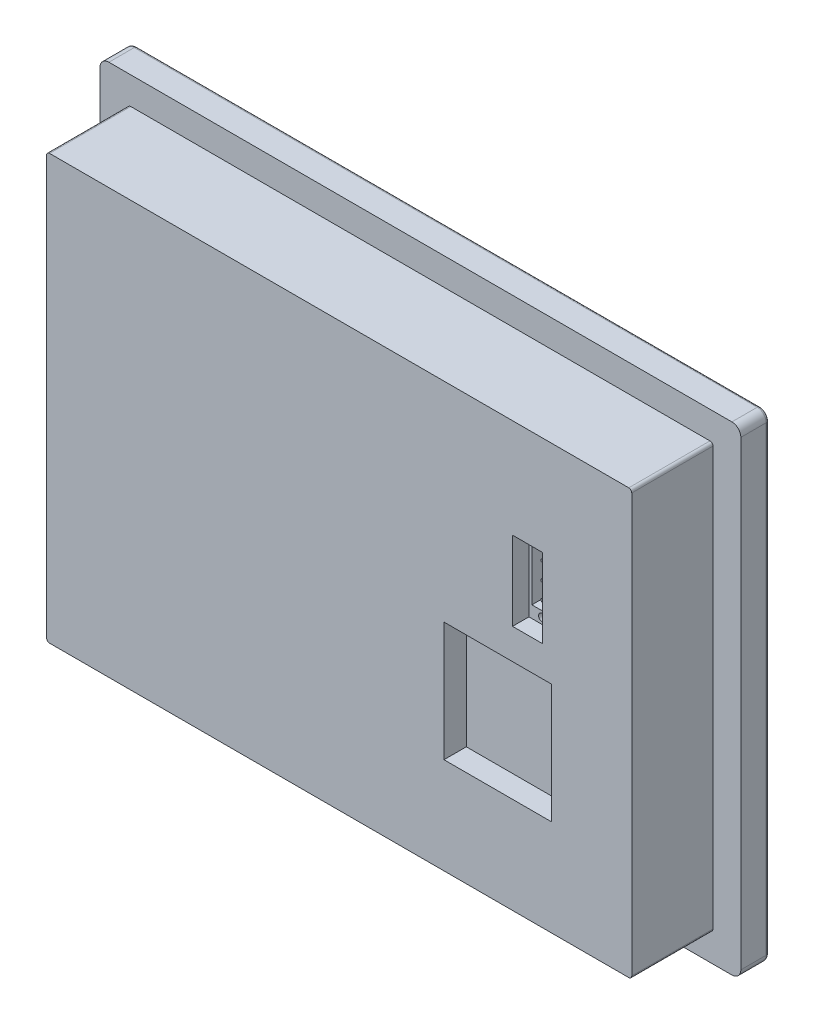
SolidWorks part; units mm, degrees
ref_plane "Ön Düzlem" through (0, 0, 0) normal (0, 0, 1) x (1, 0, 0)
ref_plane "Üst Düzlem" through (0, 0, 0) normal (0, 1, 0) x (1, 0, 0)
ref_plane "Sağ Düzlem" through (0, 0, 0) normal (1, 0, 0) x (0, 0, -1)
sketch "Çizim1" plane through (0, 0, 0) normal (0, 0, 1) x (1, 0, 0)
  line L1 (-107.5, 80.35) -> (107.5, 80.35)
  line L2 (-107.5, 80.35) -> (-107.5, -80.35)
  line L3 (-107.5, -80.35) -> (107.5, -80.35)
  line L4 (107.5, 80.35) -> (107.5, -80.35)
  line L5 (-107.5, 80.35) -> (107.5, -80.35) construction
  line L6 (-107.5, -80.35) -> (107.5, 80.35) construction
  point P0 (0, 0)
  dimension "D1" = 215
  dimension "D2" = 160.7
extrude "Yükseklik-Ekstrüzyon1" add sketch "Çizim1" along normal blind 9.5
sketch "Çizim2" plane through (0, 0, 9.5) normal (0, 0, 1) x (1, 0, 0)
  line L1 (-98.15, 71.15) -> (98.15, 71.15)
  line L2 (-98.15, 71.15) -> (-98.15, -71.15)
  line L3 (-98.15, -71.15) -> (98.15, -71.15)
  line L4 (98.15, 71.15) -> (98.15, -71.15)
  line L5 (-98.15, 71.15) -> (98.15, -71.15) construction
  line L6 (-98.15, -71.15) -> (98.15, 71.15) construction
  point P0 (0, 0)
  dimension "D1" = 196.3
  dimension "D2" = 142.3
extrude "Yükseklik-Ekstrüzyon2" add sketch "Çizim2" along normal blind 27.24
sketch "Çizim3" plane through (0, 0, 36.74) normal (0, 0, 1) x (1, 0, 0)
  line L1 (58.15, 37.9) -> (68.15, 37.9)
  line L2 (58.15, 37.9) -> (58.15, 11.4)
  line L3 (58.15, 11.4) -> (68.15, 11.4)
  line L4 (68.15, 37.9) -> (68.15, 11.4)
  line L5 (58.15, 37.9) -> (68.15, 11.4) construction
  line L6 (58.15, 11.4) -> (68.15, 37.9) construction
  line L7 (98.15, 71.15) -> (-98.15, 71.15) construction
  line L8 (98.15, -71.15) -> (98.15, 71.15) construction
  line L9 (58.65, 37.4) -> (67.65, 37.4)
  line L10 (67.65, 37.4) -> (67.65, 11.9)
  line L11 (58.65, 11.9) -> (67.65, 11.9)
  line L12 (58.65, 37.4) -> (58.65, 11.9)
  point P0 (63.15, 24.65)
  dimension "D1" = 46.5
  dimension "D2" = 35
  dimension "D3" = 10
  dimension "D4" = 26.5
  dimension "D5" = 0.5
extrude "Kes-Ekstrüzyon1" cut sketch "Çizim3" against normal blind 15
sketch "Çizim4" plane through (0, 0, 36.74) normal (0, 0, 1) x (1, 0, 0)
  line L4 (67.65, 37.4) -> (58.65, 37.4)
  line L5 (58.65, 37.4) -> (58.65, 11.9)
  line L6 (58.65, 11.9) -> (67.65, 11.9)
  line L7 (67.65, 11.9) -> (67.65, 37.4)
  line L8 (67.65, 37.4) -> (58.65, 37.4)
  line L9 (58.65, 37.4) -> (58.65, 11.9)
  line L10 (58.65, 11.9) -> (67.65, 11.9)
  line L11 (67.65, 11.9) -> (67.65, 37.4)
  dimension "D1" = 0
extrude "Kes-Ekstrüzyon2" cut sketch "Çizim4" against normal blind 5
sketch "Çizim5" plane through (0, 0, 31.74) normal (0, 0, 1) x (1, 0, 0)
  line L0 (63.15, 37.4) -> (63.15, 11.9) construction
  line L1 (67.65, 37.4) -> (58.65, 37.4) construction
  line L2 (58.65, 11.9) -> (67.65, 11.9) construction
  line L3 (63.15, 24.65) -> (67.65, 24.65) construction
  line L4 (67.65, 11.9) -> (67.65, 37.4) construction
  line L5 (59.65, 33.4) -> (59.65, 15.9)
  line L6 (59.65, 15.9) -> (66.65, 15.9) construction
  line L7 (66.65, 15.9) -> (66.65, 33.4) construction
  line L8 (66.65, 33.4) -> (59.65, 33.4) construction
  line L9 (67.65, 37.4) -> (58.65, 37.4) construction
  line L10 (58.65, 37.4) -> (58.65, 11.9) construction
  line L11 (63.65, 15.9) -> (59.65, 15.9)
  line L12 (59.65, 33.4) -> (63.65, 33.4)
  line L13 (66.65, 30.4) -> (59.65, 30.4) construction
  arc A2 (64.507, 27.525) -> (63.65, 33.4) centre (63.65, 30.4) ccw
  arc A3 (64.507, 21.775) -> (63.65, 15.9) centre (63.65, 18.9) cw
  arc A5 (64.507, 21.775) -> (64.507, 27.525) centre (63.65, 24.65) ccw
  circle A6 centre (63.15, 30.4) radius 0.5
  circle A7 centre (63.15, 18.9) radius 0.5
  circle A8 centre (63.15, 24.65) radius 0.5
  dimension "D5" = 1
  dimension "D6" = 6
  dimension "D1" = 4
  dimension "D2" = 4
  dimension "D3" = 1
  dimension "D4" = 1
extrude "Kes-Ekstrüzyon3" cut sketch "Çizim5" against normal blind 5
hole_wizard "M3 Dişli Delik1" positions "Çizim6" profile "Çizim7" tap size "M3" standard "DIN"
sketch "Çizim6" plane through (0, 0, 31.74) normal (0, 0, 1) x (1, 0, 0)
  line L0 (63.15, 37.4) -> (63.15, 33.4) construction
  line L1 (67.65, 37.4) -> (58.65, 37.4) construction
  line L2 (63.65, 33.4) -> (59.65, 33.4) construction
  line L4 (63.15, 11.9) -> (63.15, 15.9) construction
  line L5 (58.65, 11.9) -> (67.65, 11.9) construction
  line L6 (59.65, 15.9) -> (63.65, 15.9) construction
  point P5 (63.15, 35.4)
  point P23 (63.15, 13.9)
cosmetic thread "Delik Dişi1" parameters "D1"=6, "D2"=3
cosmetic thread "Delik Dişi2" parameters "D1"=6, "D2"=3
sketch "Çizim7" plane through (63.15, 35.4, 31.74) normal (1, 0, 0) x (0, -1, 0)
  line L0 (0, 0) -> (0, 9.2511)
  line L1 (0, 9.2511) -> (1.25, 8.5)
  line L2 (1.25, 8.5) -> (1.25, 0)
  line L5 (1.25, 0) -> (0, 0)
  line L10 (0, 9.2511) -> (-1.25, 8.5) construction
  line L11 (0, -6.35) -> (0, 107.95) construction
  dimension "Tap Drill Dia." = 2.5
  dimension "Tap Drill Depth" = 8.5
  dimension "Drill Angle" = 118
sketch "Çizim8" plane through (0, 0, 0) normal (0, 0, -1) x (-1, 0, 0)
  line L1 (-77.5, 43) -> (77.5, 43)
  line L2 (-77.5, 43) -> (-77.5, -43)
  line L3 (-77.5, -43) -> (77.5, -43)
  line L4 (77.5, 43) -> (77.5, -43)
  line L5 (-77.5, 43) -> (77.5, -43) construction
  line L6 (-77.5, -43) -> (77.5, 43) construction
  point P0 (0, 0)
  dimension "D1" = 155
  dimension "D2" = 86
extrude "Kes-Ekstrüzyon4" cut sketch "Çizim8" against normal blind 0.05
sketch "Çizim9" plane through (0, 0, 0) normal (0, 0, -1) x (-1, 0, 0)
  line L0 (-88, 61) -> (88, 61)
  line L1 (-88, 60) -> (88, 60)
  line L2 (-91, 57) -> (-91, -60)
  line L3 (-91, -60) -> (88, -60)
  line L4 (91, 57) -> (91, -57)
  line L5 (-91, 60) -> (91, -60) construction
  line L6 (-91, -60) -> (91, 60) construction
  line L7 (92, 57) -> (92, -57)
  line L8 (-92, -61) -> (88, -61)
  line L9 (-92, 57) -> (-92, -61)
  arc A0 (-88, 60) -> (-91, 57) centre (-88, 57) ccw
  arc A1 (91, 57) -> (88, 60) centre (88, 57) ccw
  arc A2 (88, -60) -> (91, -57) centre (88, -57) ccw
  arc A3 (92, 57) -> (88, 61) centre (88, 57) ccw
  arc A4 (88, -61) -> (92, -57) centre (88, -57) ccw
  arc A5 (-88, 61) -> (-92, 57) centre (-88, 57) ccw
  point P0 (0, 0)
  dimension "D3" = 3
  dimension "D1" = 182
  dimension "D2" = 120
  dimension "D4" = 1
extrude "Kes-Ekstrüzyon5" cut sketch "Çizim9" against normal blind 0.005
fillet "Radyus1" radius 3 4 edges at (107.5, -80.35, 4.75) (-107.5, -80.35, 4.75) (-107.5, 80.35, 4.75) (107.5, 80.35, 4.75)
fillet "Radyus2" radius 1 8 edges at (106.6213, 79.4713, 0) (107.5, 0, 0) (106.6213, -79.4713, 0) (0, -80.35, 0) (-106.6213, -79.4713, 0) (-107.5, 0, 0) (-106.6213, 79.4713, 0) (0, 80.35, 0)
sketch "Çizim10" plane through (0, 0, 36.74) normal (0, 0, 1) x (1, 0, 0)
  line L0 (98.15, -71.15) -> (98.15, 71.15) construction
  line L1 (35.15, 1.15) -> (71.15, 1.15)
  line L2 (35.15, 1.15) -> (35.15, -38.85)
  line L3 (35.15, -38.85) -> (71.15, -38.85)
  line L4 (71.15, 1.15) -> (71.15, -38.85)
  line L5 (-98.15, -71.15) -> (98.15, -71.15) construction
  dimension "D1" = 27
  dimension "D2" = 32.3
  dimension "D3" = 36
  dimension "D4" = 40
extrude "Kes-Ekstrüzyon6" cut sketch "Çizim10" against normal blind 7.5
fillet "Radyus3" radius 1 4 edges at (-98.15, -71.15, 23.12) (98.15, -71.15, 23.12) (98.15, 71.15, 23.12) (-98.15, 71.15, 23.12)
